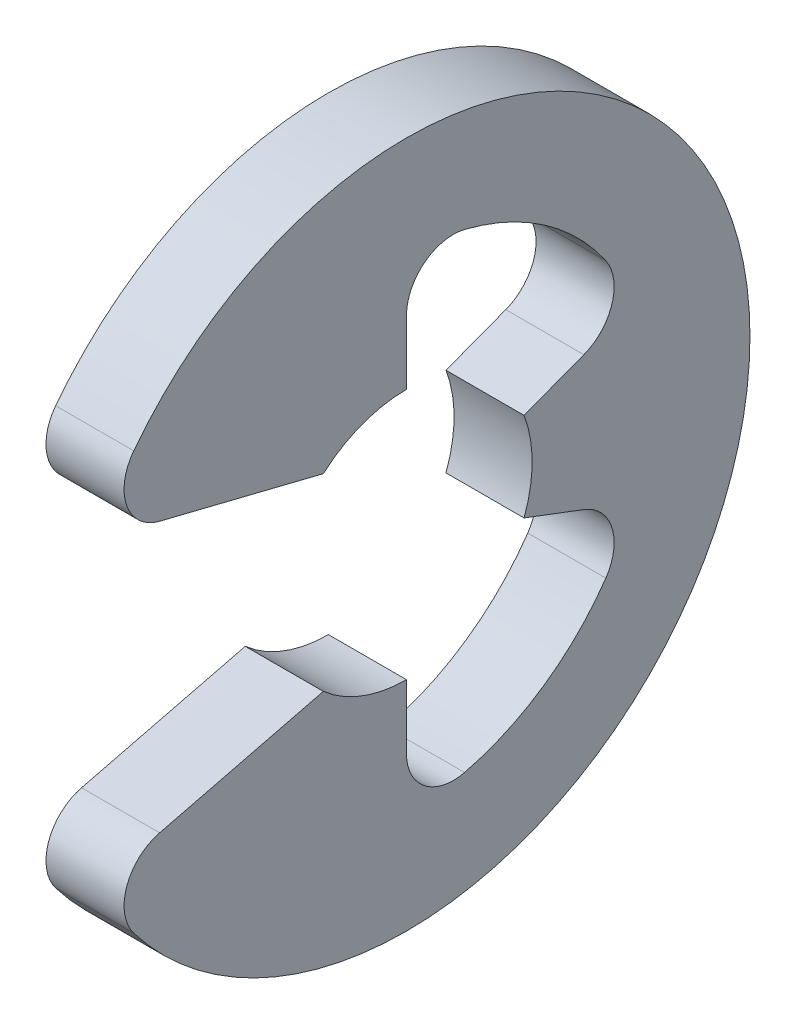
SolidWorks part; units mm, degrees
material "AISI 316 Annealed Stainless Steel Bar (SS)"
ref_plane "Front" through (0, 0, 0) normal (0, 0, 1) x (1, 0, 0)
ref_plane "Top" through (0, 0, 0) normal (0, 1, 0) x (1, 0, 0)
ref_plane "Right" through (0, 0, 0) normal (1, 0, 0) x (0, 0, -1)
sketch "Sketch1" plane through (0, 0, 0) normal (1, 0, 0) x (0, 0, -1)
  line L0 (-1.9782, -0.9627) -> (-0.5325, -0.6038)
  line L1 (-1.9782, 0.9627) -> (-0.5325, 0.6037)
  line L2 (0, -0.805) -> (0, -1.551)
  line L3 (0, 0.805) -> (0, 1.551)
  line L4 (0.753, -0.2846) -> (1.4508, -0.5483)
  line L5 (0.753, 0.2846) -> (1.4508, 0.5483)
  line L6 (0, 0) -> (-2.4, 0) construction
  line L7 (0.753, 0.2846) -> (0.753, -0.2846) construction
  line L8 (0, -0.805) -> (-0.5325, -0.6038) construction
  circle A1 centre (0, 0) radius 2.4 construction
  circle A2 centre (0, 0) radius 0.805 construction
  arc A3 (-1.9782, -0.9627) -> (-1.9782, 0.9627) centre (0, 0) ccw
  arc A4 (-0.5325, -0.6038) -> (0, -0.805) centre (0, 0) ccw
  arc A5 (-0.5325, 0.6037) -> (0, 0.805) centre (0, 0) cw
  arc A6 (0.753, 0.2846) -> (0.753, -0.2846) centre (0, 0) cw
  arc A7 (0, -1.551) -> (1.4508, -0.5483) centre (0, 0) ccw
  arc A8 (1.4508, 0.5483) -> (0, 1.551) centre (0, 0) ccw
  dimension "D" = 1.61
  dimension "D1" = 1.551
  dimension "OD" = 4.4
  dimension "D2" = 0.9153
  dimension "D3" = 1.2075
extrude "Extrude1" add sketch "Sketch1" along normal mid plane 0.5
fillet "Fillet1" radius 0.3 6 edges at (0, -1.551, 0) (0, 1.551, 0) (0, -0.9627, 1.9782) (0, 0.9627, 1.9782) (0, -0.5483, -1.4508) (0, 0.5483, -1.4508)
sketch "Sketch3" plane through (0, 0, 0) normal (0, 1, 0) x (1, 0, 0)
  line L0 (0.27, 1.25) -> (0.27, 0.95)
  line L1 (0.27, 0.95) -> (-0.27, 0.95)
  line L2 (-0.27, 0.95) -> (-0.27, 1.25)
  line L3 (-0.27, 1.25) -> (-3.78, 1.25)
  line L4 (1.62, 0) -> (1.62, 0.95)
  line L5 (-3.78, 1.25) -> (-3.78, 0)
  line L6 (-3.78, 0) -> (1.62, 0)
  line L8 (1.62, 0) -> (1.62, 1.25) construction
  line L9 (1.62, 1.25) -> (0.27, 1.25) construction
  line L10 (1.62, 0) -> (17.2631, 0) construction
  line L11 (1.62, 0.95) -> (1.32, 1.25)
  line L12 (1.32, 1.25) -> (0.27, 1.25)
  point P2 (0, 0.95)
  dimension "D2" = 5.4
  dimension "D1" = 1.35
  dimension "D3" = 45
revolve "Revolve2" [suppressed] add sketch "Sketch3" angle 360 about L10
equation "\"D2@Sketch3\" = \"W@Sketch3\"*10"
equation "\"D1@Sketch3\" = \"D2@Sketch3\"/4"
equation "\"D1@Sketch1\" = (\"OD@Sketch1\"+\"D@Sketch1\")/3.875"
equation "\"D3@Sketch1\" = \"D@Sketch1\"*.75"
equation "\"D1@Fillet1\" = \"D1@Extrude1\"*.6"
